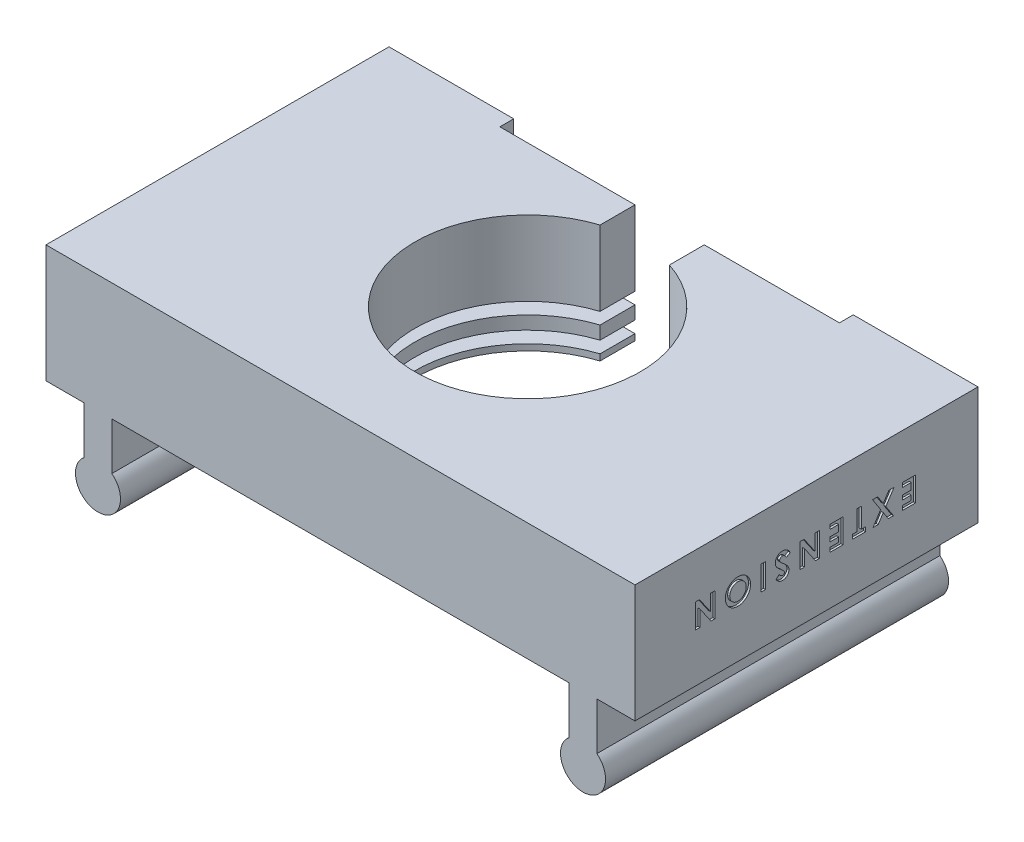
SolidWorks part; units mm, degrees
ref_plane "Plan de face" through (0, 0, 0) normal (0, 0, 1) x (1, 0, 0)
ref_plane "Plan de dessus" through (0, 0, 0) normal (0, 1, 0) x (1, 0, 0)
ref_plane "Plan de droite" through (0, 0, 0) normal (1, 0, 0) x (0, 0, -1)
sketch "Esquisse1" plane through (0, 0, 0) normal (0, 0, 1) x (1, 0, 0)
  line L1 (-42.5, -8.5) -> (42.5, -8.5)
  line L2 (-42.5, -8.5) -> (-42.5, 8.5)
  line L3 (-42.5, 8.5) -> (42.5, 8.5)
  line L4 (42.5, -8.5) -> (42.5, 8.5)
  line L5 (-42.5, -8.5) -> (42.5, 8.5) construction
  line L6 (-42.5, 8.5) -> (42.5, -8.5) construction
  point P0 (0, 0)
  dimension "D1" = 85
  dimension "D2" = 17
extrude "Boss.-Extru.1" add sketch "Esquisse1" along normal blind 49.5
sketch "Esquisse2" plane through (0, 0, 0) normal (0, 0, -1) x (-1, 0, 0)
  line L0 (42.5, -8.5) -> (-42.5, -8.5) construction
  line L1 (24.5, 8.5) -> (-24.5, 8.5)
  line L2 (24.5, 8.5) -> (24.5, -8.5)
  line L3 (24.5, -8.5) -> (-24.5, -8.5)
  line L4 (-24.5, 8.5) -> (-24.5, -8.5)
  line L5 (24.5, 8.5) -> (-24.5, -8.5) construction
  line L6 (24.5, -8.5) -> (-24.5, 8.5) construction
  point P0 (0, 0)
  dimension "D1" = 49
extrude "Enlèv. mat.-Extru.1" cut sketch "Esquisse2" against normal blind 2
sketch "Esquisse3" plane through (0, 0, 2) normal (0, 0, -1) x (-1, 0, 0)
  line L0 (-24.5, -8.5) -> (24.5, -8.5) construction
  line L1 (21, -5.9) -> (-21, -5.9)
  line L2 (21, -5.9) -> (21, -7.6)
  line L3 (21, -7.6) -> (-21, -7.6)
  line L4 (-21, -5.9) -> (-21, -7.6)
  line L5 (21, -5.9) -> (-21, -7.6) construction
  line L6 (21, -7.6) -> (-21, -5.9) construction
  line L7 (21, -2.3) -> (21, -4)
  line L8 (21, -2.3) -> (-21, -2.3)
  line L9 (-21, -2.3) -> (-21, -4)
  line L10 (21, -4) -> (-21, -4)
  point P0 (0, -6.75)
  dimension "D1" = 42
  dimension "D2" = 0.9
  dimension "D3" = 1.7
  dimension "D5" = 1.9
  dimension "D4" = 2
extrude "Enlèv. mat.-Extru.2" cut sketch "Esquisse3" against normal blind 45
sketch "Esquisse4" plane through (0, -8.5, 0) normal (0, -1, 0) x (1, 0, 0)
  line L0 (24.5, 2) -> (-24.5, 2) construction
  circle A0 centre (0, 22.5) radius 16.25
  dimension "D1" = 32.5
  dimension "D2" = 20.5
  dimension "D3" = 24.5
extrude "Enlèv. mat.-Extru.3" cut sketch "Esquisse4" against normal through all
sketch "Esquisse5" plane through (0, -8.5, 0) normal (0, -1, 0) x (1, 0, 0)
  line L0 (-5, 2) -> (5, 2)
  line L1 (24.5, 2) -> (-24.5, 2) construction
  line L2 (5, 2) -> (5, 7.0384)
  line L3 (5, 7.0384) -> (-5, 7.0384)
  line L4 (-5, 7.0384) -> (-5, 2)
  circle A0 centre (0, 22.5) radius 16.25 construction
  dimension "D1" = 10
extrude "Enlèv. mat.-Extru.4" cut sketch "Esquisse5" against normal through all
sketch "Esquisse7" plane through (0, 0, 0) normal (0, 0, -1) x (-1, 0, 0)
  line L0 (33, -8.5) -> (33, -15.34)
  line L1 (42.5, -8.5) -> (24.5, -8.5) construction
  line L2 (33, -8.5) -> (37, -8.5)
  line L3 (37, -8.5) -> (37, -15.34)
  line L4 (0, 0) -> (0, -24.3357) construction
  line L5 (-33, -8.5) -> (-37, -8.5)
  line L6 (-33, -8.5) -> (-33, -15.34)
  line L7 (-37, -8.5) -> (-37, -15.34)
  arc A0 (33, -15.34) -> (37, -15.34) centre (35, -17.9017) ccw
  arc A1 (-33, -15.34) -> (-37, -15.34) centre (-35, -17.9017) cw
  dimension "D2" = 3.25
  dimension "D1" = 4
  dimension "D3" = 6.84
  dimension "D4" = 6.84
  dimension "D5" = 5.5
extrude "Boss.-Extru.2" add sketch "Esquisse7" against normal up to surface (49.5 mm away) up to face at (0, 0, 49.5)
sketch "Esquisse9" plane through (42.5, 0, 0) normal (1, 0, 0) x (0, 0, -1)
  line L0 (0, 2) -> (-49.5, 2) construction
  line L1 (0, -8.5) -> (0, 8.5) construction
  line L2 (-49.5, -8.5) -> (-49.5, 8.5) construction
  line L3 (-49.5, -8.5) -> (0, -8.5) construction
  text T0 "<b>EXTENSION</b>" font "Century Gothic" height 3.5
  dimension "D1" = 10.5
extrude "Enlèv. mat.-Extru.6" cut sketch "Esquisse9" against normal blind 0.3
